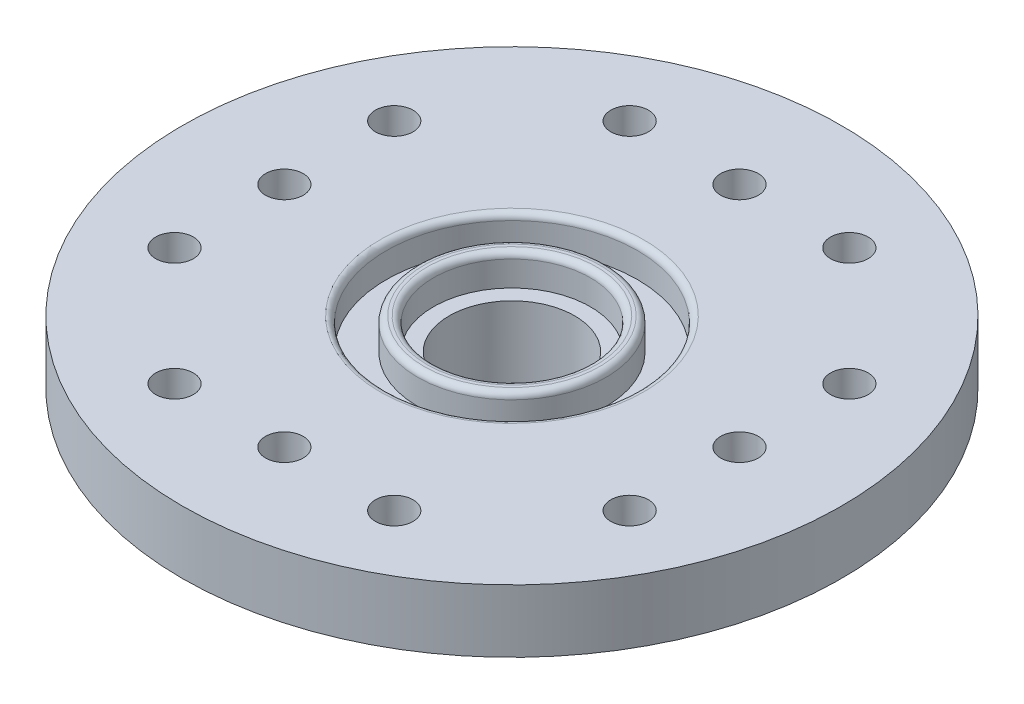
SolidWorks part; units mm, degrees
ref_plane "Alzado" through (0, 0, 0) normal (0, 0, 1) x (1, 0, 0)
ref_plane "Planta" through (0, 0, 0) normal (0, 1, 0) x (1, 0, 0)
ref_plane "Vista lateral" through (0, 0, 0) normal (1, 0, 0) x (0, 0, -1)
sketch "Croquis1" plane through (0, 0, 0) normal (0, 1, 0) x (1, 0, 0)
  circle A0 centre (0, 0) radius 10.5
  dimension "D1" = 21
extrude "Saliente-Extruir1" add sketch "Croquis1" along normal blind 2
sketch "Croquis2" plane through (0, 0, 0) normal (0, -1, 0) x (1, 0, 0)
  circle A0 centre (0, 0) radius 4
  circle A1 centre (0, 0) radius 2
  dimension "D1" = 2
extrude "Saliente-Extruir2" add sketch "Croquis2" along normal blind 3
fillet "Redondeo1" radius 1 1 edges at (0, -3, -4)
sketch "Croquis3" plane through (0, 2, 0) normal (0, 1, 0) x (1, 0, 0)
  circle A3 centre (0, 0) radius 3
  circle A4 centre (0, 0) radius 4
  dimension "D1" = 6
  dimension "D2" = 8
extrude "Cortar-Extruir1" cut sketch "Croquis3" against normal blind 1
sketch "Croquis4" plane through (0, 2, 0) normal (0, 1, 0) x (1, 0, 0)
  circle A2 centre (0, 0) radius 2
  circle A3 centre (0, 0) radius 2
  dimension "D1" = 1
extrude "Cortar-Extruir2" cut sketch "Croquis4" against normal blind 3
sketch "Croquis5" plane through (0, 2, 0) normal (0, 1, 0) x (1, 0, 0)
  circle A4 centre (0, 0) radius 2.5
  circle A5 centre (0, 0) radius 2.5
  dimension "D1" = 0.5
extrude "Cortar-Extruir3" cut sketch "Croquis5" against normal blind 1
sketch "Croquis6" plane through (0, 2, 0) normal (0, 1, 0) x (1, 0, 0)
  line L0 (0, 4) -> (0, 10.5) construction
  line L1 (-5.7527, 7.25) -> (5.838, 7.25) construction
  circle A0 centre (0, 0) radius 7.25 construction
  circle A1 centre (0, 0) radius 4 construction
  circle A2 centre (0, 0) radius 4 construction
  circle A3 centre (0, 0) radius 10.5 construction
  circle A4 centre (0, 7.25) radius 0.6
  circle A5 centre (3.5, 7.25) radius 0.6
  circle A6 centre (-3.5, 7.25) radius 0.6
  dimension "D1" = 14.5
  dimension "D2" = 1.2
  dimension "D3" = 2
  dimension "D4" = 2
extrude "Cortar-Extruir4" cut sketch "Croquis6" against normal through all
pattern_circular "MatrizC1" count 4 over 360 about axis through (0, 0, 0) along (0, 1, 0) of "Cortar-Extruir4"
fillet "Redondeo2" radius 0.2 3 edges at (0, 2, 2.5) (0, 2, 3) (0, 2, 4)
